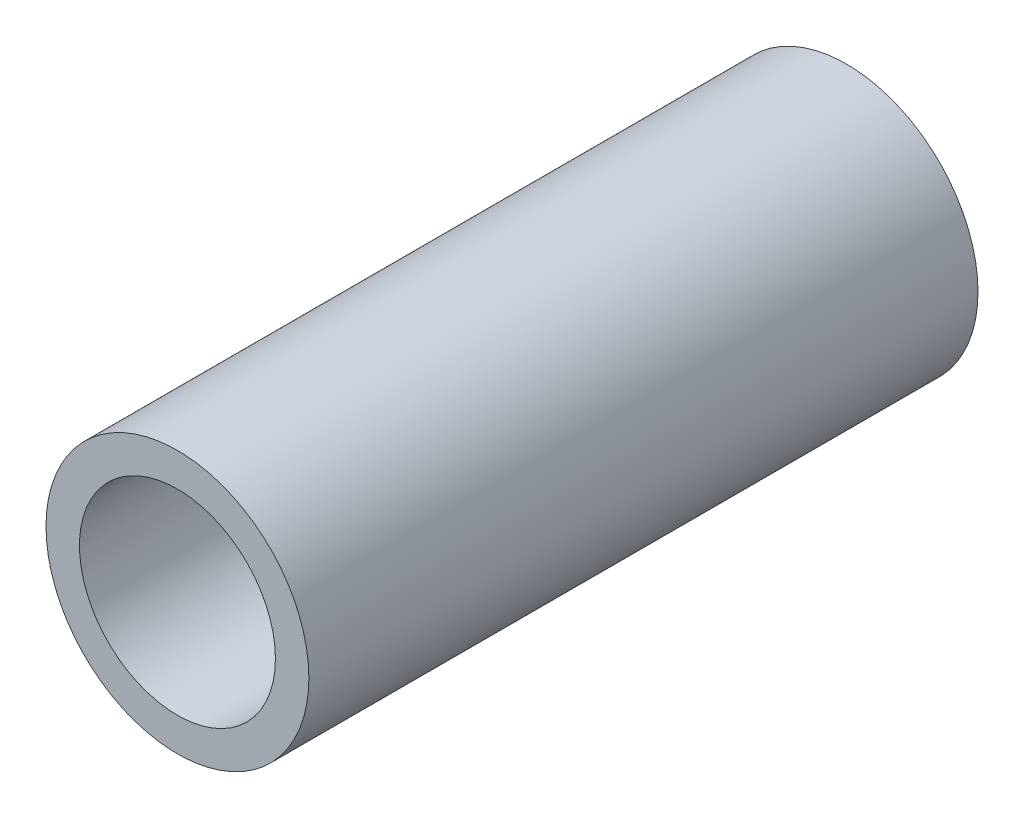
SolidWorks part; units mm, degrees
ref_plane "Front Plane" through (0, 0, 0) normal (0, 0, 1) x (1, 0, 0)
ref_plane "Top Plane" through (0, 0, 0) normal (0, 1, 0) x (1, 0, 0)
ref_plane "Right Plane" through (0, 0, 0) normal (1, 0, 0) x (0, 0, -1)
sketch "Sketch1" plane through (0, 0, 0) normal (0, 0, 1) x (1, 0, 0)
  circle A0 centre (0, 0) radius 5.5
  circle A1 centre (0, 0) radius 4.1
  dimension "D1" = 8.2
  dimension "D2" = 11
extrude "Boss-Extrude1" add sketch "Sketch1" along normal blind 28
